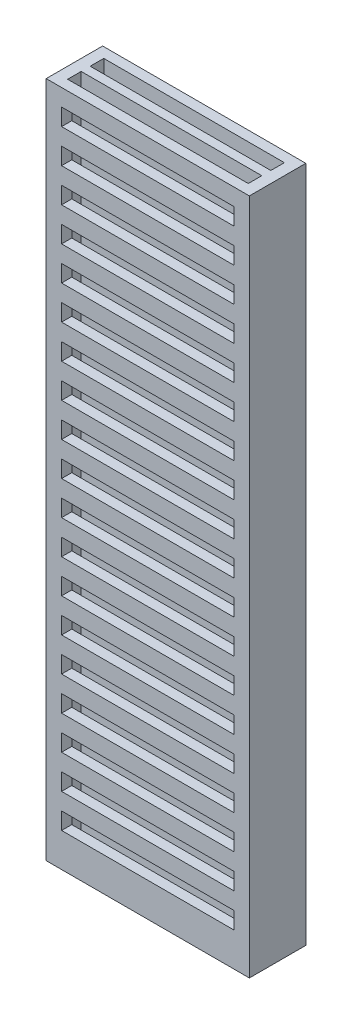
SolidWorks part; units mm, degrees
ref_plane "Front Plane" through (0, 0, 0) normal (0, 0, 1) x (1, 0, 0)
ref_plane "Top Plane" through (0, 0, 0) normal (0, 1, 0) x (1, 0, 0)
ref_plane "Right Plane" through (0, 0, 0) normal (1, 0, 0) x (0, 0, -1)
sketch "Sketch1" plane through (0, 0, 0) normal (0, 1, 0) x (1, 0, 0)
  line L1 (-4.5, -1.25) -> (4.5, -1.25)
  line L2 (-4.5, -1.25) -> (-4.5, 1.25)
  line L3 (-4.5, 1.25) -> (4.5, 1.25)
  line L4 (4.5, -1.25) -> (4.5, 1.25)
  line L5 (-4.5, -1.25) -> (4.5, 1.25) construction
  line L6 (-4.5, 1.25) -> (4.5, -1.25) construction
  point P0 (0, 0)
  dimension "D1" = 9
  dimension "D2" = 2.5
extrude "Boss-Extrude1" add sketch "Sketch1" along normal mid plane 30
sketch "Sketch2" plane through (0, 15, 0) normal (0, 1, 0) x (1, 0, 0)
  line L1 (-4, 0.2) -> (4, 0.2)
  line L2 (-4, 0.2) -> (-4, 0.8)
  line L3 (-4, 0.8) -> (4, 0.8)
  line L4 (4, 0.2) -> (4, 0.8)
  line L5 (-4, 0.2) -> (4, 0.8) construction
  line L6 (-4, 0.8) -> (4, 0.2) construction
  point P0 (0, 0.5)
  dimension "D1" = 0.6
  dimension "D2" = 8
  dimension "D3" = 0
  dimension "D4" = 0.5
extrude "Cut-Extrude1" cut sketch "Sketch2" against normal through all and the other way through all
mirror "Mirror1" about plane through (0, 0, 0) normal (0, 0, 1) of "Cut-Extrude1"
sketch "Sketch3" plane through (0, 0, 1.25) normal (0, 0, 1) x (1, 0, 0)
  line L0 (0, -1.65) -> (0, 1.65) construction
  line L1 (-3.8171, 13.5) -> (3.8171, 13.5)
  line L2 (-3.8171, 13.5) -> (-3.8171, 14.25)
  line L3 (-3.8171, 14.25) -> (3.8171, 14.25)
  line L4 (3.8171, 13.5) -> (3.8171, 14.25)
  line L5 (-3.8171, 13.5) -> (3.8171, 14.25) construction
  line L6 (-3.8171, 14.25) -> (3.8171, 13.5) construction
  line L7 (-4.5, 15) -> (4.5, 15) construction
  point P0 (0, 13.875)
  dimension "D1" = 0.75
  dimension "D2" = 0.75
extrude "Cut-Extrude2" cut sketch "Sketch3" against normal up to next (0.45 mm away)
pattern_linear "LPattern1" count 19 spacing 1.5 along (0, -1, 0) of "Cut-Extrude2"
mirror "Mirror2" about plane through (0, 0, 0) normal (0, 0, 1) of "LPattern1", "Cut-Extrude2"
